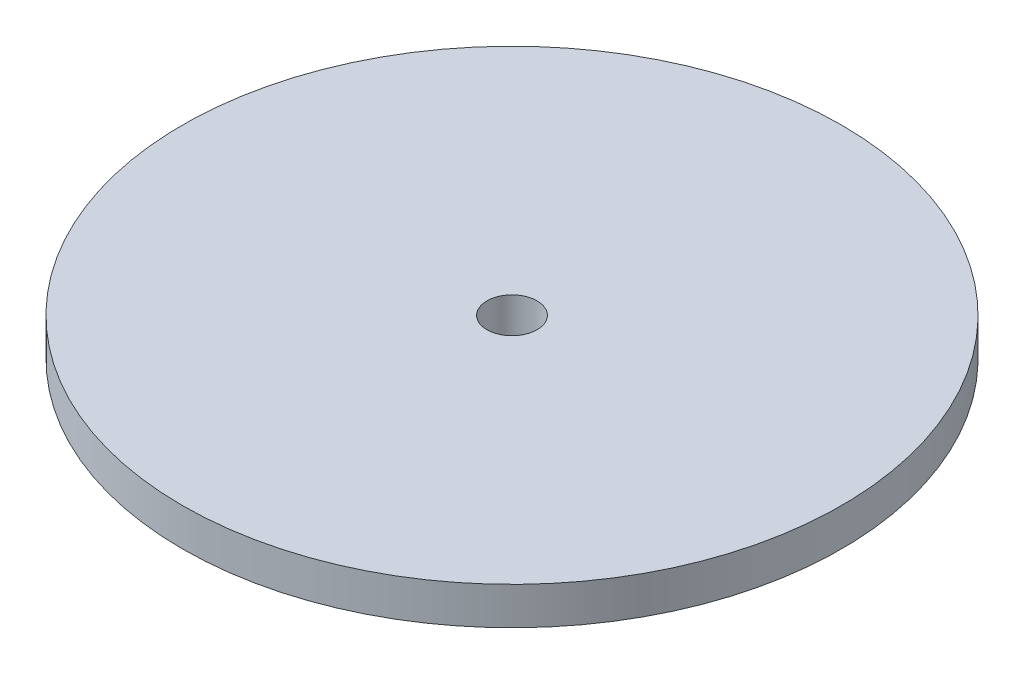
SolidWorks part; units mm, degrees
ref_plane "Front Plane" through (0, 0, 0) normal (0, 0, 1) x (1, 0, 0)
ref_plane "Top Plane" through (0, 0, 0) normal (0, 1, 0) x (1, 0, 0)
ref_plane "Right Plane" through (0, 0, 0) normal (1, 0, 0) x (0, 0, -1)
sketch "Sketch1" plane through (0, 0, 0) normal (0, 1, 0) x (1, 0, 0)
  circle A0 centre (0, 0) radius 10.5
  circle A1 centre (0, 0) radius 1
  dimension "D1" = 21
  dimension "D2" = 2
extrude "Boss-Extrude1" add sketch "Sketch1" along normal blind 1.5
sketch "Sketch2" plane through (0, 1.5, 0) normal (0, 1, 0) x (1, 0, 0)
  circle A0 centre (0, 0) radius 13.15
  circle A1 centre (0, 0) radius 10.5
  circle A2 centre (0, 0) radius 10.5
  circle A3 centre (0, 0) radius 1 construction
  circle A4 centre (0, 0) radius 1
  circle M2 centre (0, 0) radius 10.5
  circle M3 centre (0, 0) radius 1
  dimension "D2" = 26.3
  dimension "D1" = 0
extrude "Boss-Extrude2" add sketch "Sketch2" along normal blind 1.5 contours M2 M3 | A0 M2
sketch "Sketch4" plane through (0, 0, 0) normal (0, -1, 0) x (1, 0, 0)
  circle A1 centre (0, 0) radius 10.5
  circle A2 centre (0, 0) radius 10.5
  dimension "D1" = 0
extrude "Cut-Extrude1" cut sketch "Sketch4" against normal blind 1.5
